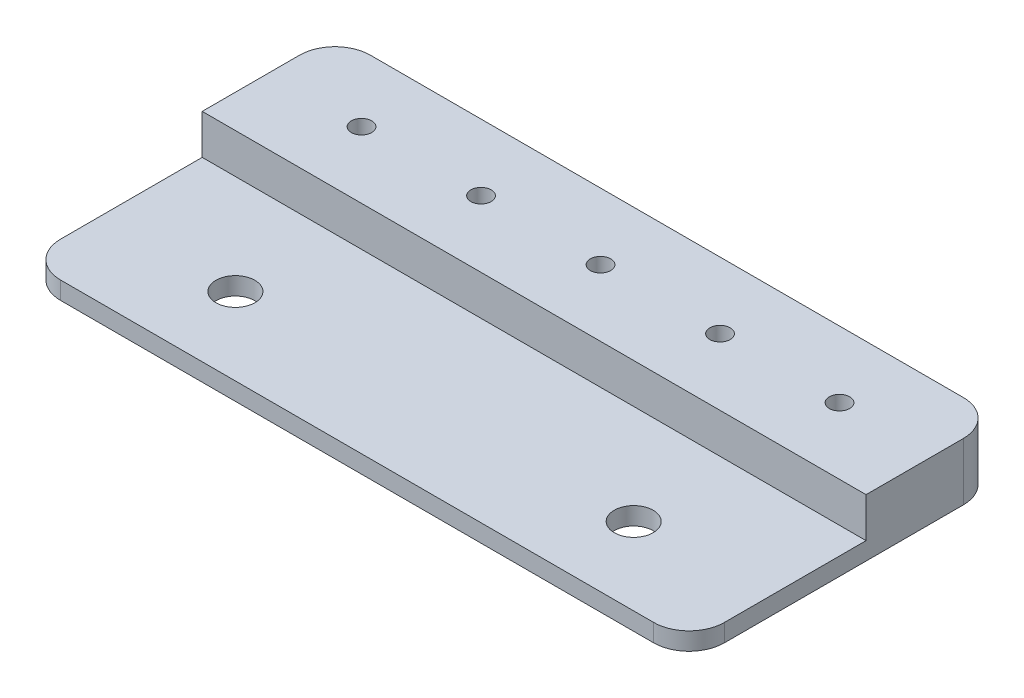
SolidWorks part; units mm, degrees
ref_plane "Front Plane" through (0, 0, 0) normal (0, 0, 1) x (1, 0, 0)
ref_plane "Top Plane" through (0, 0, 0) normal (0, 1, 0) x (1, 0, 0)
ref_plane "Right Plane" through (0, 0, 0) normal (1, 0, 0) x (0, 0, -1)
sketch "Sketch1" plane through (0, 0, 0) normal (0, 1, 0) x (1, 0, 0)
  line L0 (-75, -17.5) -> (75, -17.5) construction
  line L1 (-67, 35) -> (67, 35)
  line L2 (-75, 27) -> (-75, -27)
  line L3 (-67, -35) -> (67, -35)
  line L4 (75, 27) -> (75, -27)
  line L5 (-75, 35) -> (75, -35) construction
  line L6 (-75, -35) -> (75, 35) construction
  line L7 (-75, 5) -> (75, 5) construction
  arc A0 (-67, -35) -> (-75, -27) centre (-67, -27) cw
  arc A1 (67, -35) -> (75, -27) centre (67, -27) ccw
  arc A2 (75, 27) -> (67, 35) centre (67, 27) ccw
  arc A3 (-67, 35) -> (-75, 27) centre (-67, 27) ccw
  circle A4 centre (-45, -17.5) radius 4.4
  circle A5 centre (45, -17.5) radius 4.4
  point P0 (0, 0)
  dimension "D3" = 8
  dimension "D6" = 30
  dimension "D1" = 70
  dimension "D2" = 150
  dimension "D4" = 40
  dimension "D5" = 22.5
  dimension "D7" = 30
extrude "Boss-Extrude1" add sketch "Sketch1" against normal blind 4
sketch "Sketch2" plane through (0, 0, 0) normal (0, 1, 0) x (1, 0, 0)
  line L0 (-75, 5) -> (75, 5)
  line L1 (-75, 27) -> (-75, -27) construction
  line L2 (75, -27) -> (75, 27) construction
  line L3 (67, 35) -> (-67, 35) construction
  line L4 (-75, 5) -> (-75, 27)
  line L5 (-67, 35) -> (67, 35)
  line L6 (75, 27) -> (75, 5)
  arc A0 (75, 27) -> (67, 35) centre (67, 27) ccw
  arc A1 (-75, 27) -> (-67, 35) centre (-67, 27) cw
  dimension "D2" = 8
  dimension "D1" = 30
extrude "Boss-Extrude2" add sketch "Sketch2" along normal blind 9
sketch "Sketch3" plane through (0, 9, 0) normal (0, 1, 0) x (1, 0, 0)
  line L0 (-75, 20) -> (75, 20) construction
  line L1 (-75, 27) -> (-75, 5) construction
  line L2 (75, 5) -> (75, 27) construction
  line L3 (67, 35) -> (-67, 35) construction
  circle A0 centre (-54, 20) radius 2.3
  circle A1 centre (-27, 20) radius 2.3
  circle A2 centre (0, 20) radius 2.3
  circle A3 centre (27, 20) radius 2.3
  circle A4 centre (54, 20) radius 2.3
  dimension "D2" = 21
  dimension "D3" = 5
  dimension "D1" = 15
extrude "Cut-Extrude1" cut sketch "Sketch3" against normal up to surface (13 mm away) up to face at (45, -4, 21.9)
